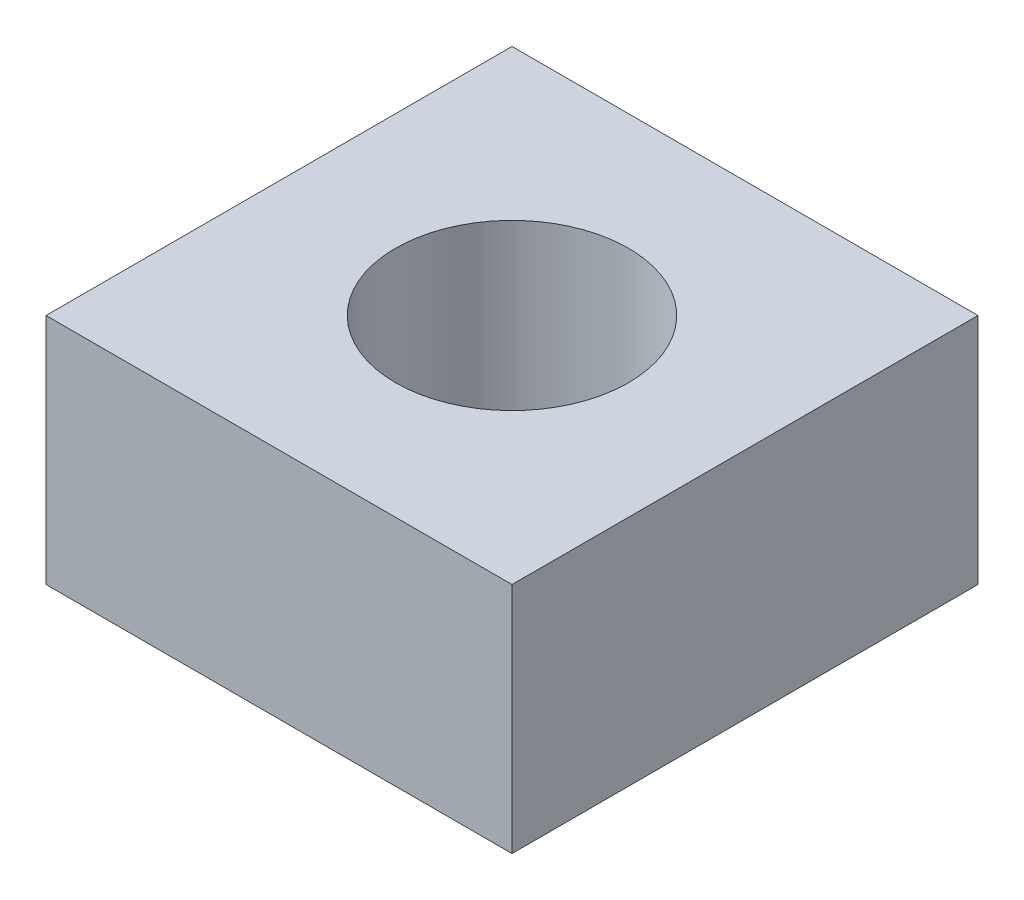
SolidWorks part; units mm, degrees
ref_plane "Front Plane" through (0, 0, 0) normal (0, 0, 1) x (1, 0, 0)
ref_plane "Top Plane" through (0, 0, 0) normal (0, 1, 0) x (1, 0, 0)
ref_plane "Right Plane" through (0, 0, 0) normal (1, 0, 0) x (0, 0, -1)
sketch "Sketch1" plane through (0, 0, 0) normal (0, 1, 0) x (1, 0, 0)
  line L1 (-10, 10) -> (10, 10)
  line L2 (-10, 10) -> (-10, -10)
  line L3 (-10, -10) -> (10, -10)
  line L4 (10, 10) -> (10, -10)
  line L5 (-10, 10) -> (10, -10) construction
  line L6 (-10, -10) -> (10, 10) construction
  circle A0 centre (0, 0) radius 5
  point P0 (0, 0)
  dimension "D2" = 10
  dimension "D1" = 20
extrude "Boss-Extrude1" add sketch "Sketch1" along normal blind 10
